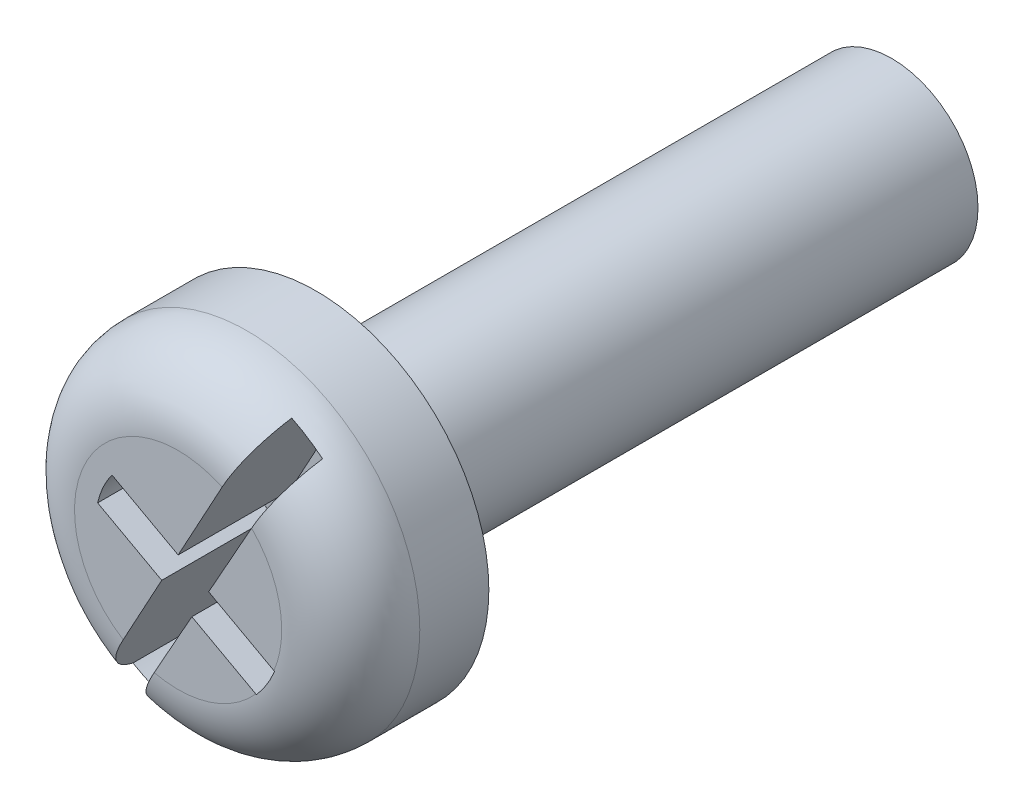
SolidWorks part; units mm, degrees
material "Stop odlewniczy stali"
ref_plane "Płaszczyzna przednia" through (0, 0, 0) normal (0, 0, 1) x (1, 0, 0)
ref_plane "Płaszczyzna górna" through (0, 0, 0) normal (0, 1, 0) x (1, 0, 0)
ref_plane "Płaszczyzna prawa" through (0, 0, 0) normal (1, 0, 0) x (0, 0, -1)
sketch "Szkic1" plane through (0, 0, 0) normal (0, 0, 1) x (1, 0, 0)
  circle A0 centre (-1.8605, 2.7321) radius 3
  dimension "D1" = 6
extrude "Dodanie-wyciągnięcie2" add sketch "Szkic1" along normal blind 2.4
sketch "Szkic2" plane through (0, 0, 0) normal (0, 0, -1) x (-1, 0, 0)
  circle A0 centre (1.8605, 2.7321) radius 1.5
extrude "Dodanie-wyciągnięcie3" add sketch "Szkic2" along normal blind 10
fillet "Zaokrąglenie2" radius 1.2 1 edges at (1.1395, 2.7321, 2.4)
sketch "Szkic3" plane through (0, 0, 2.4) normal (0, 0, 1) x (1, 0, 0)
  line L0 (-1.8595, 2.9591) -> (-0.5756, 5.3165)
  line L1 (-1.8595, 2.9591) -> (-3.0095, 3.5874)
  line L2 (-3.3345, 0.2508) -> (-2.1451, 2.4347)
  line L3 (-2.8199, 0.0102) -> (-1.6213, 2.1486)
  line L4 (-0.184, 2.0436) -> (-1.3294, 2.6694)
  line L5 (-0.4992, 1.5357) -> (-1.6213, 2.1486)
  line L6 (-1.3294, 2.6694) -> (-0.0393, 4.9711)
  line L7 (-2.1451, 2.4347) -> (-3.2587, 3.0429)
  arc A2 (-3.0095, 3.5874) -> (-3.2587, 3.0429) centre (-1.8605, 2.7321) ccw
  arc A3 (-0.0393, 4.9711) -> (-0.5756, 5.3165) centre (-1.8605, 2.7321) ccw
  arc A4 (-3.3345, 0.2508) -> (-2.8199, 0.0102) centre (-1.8605, 2.7321) ccw
  arc A6 (-0.4992, 1.5357) -> (-0.184, 2.0436) centre (-1.8605, 2.7321) ccw
extrude "Wytnij-wyciągnięcie1" cut sketch "Szkic3" against normal blind 1.94
